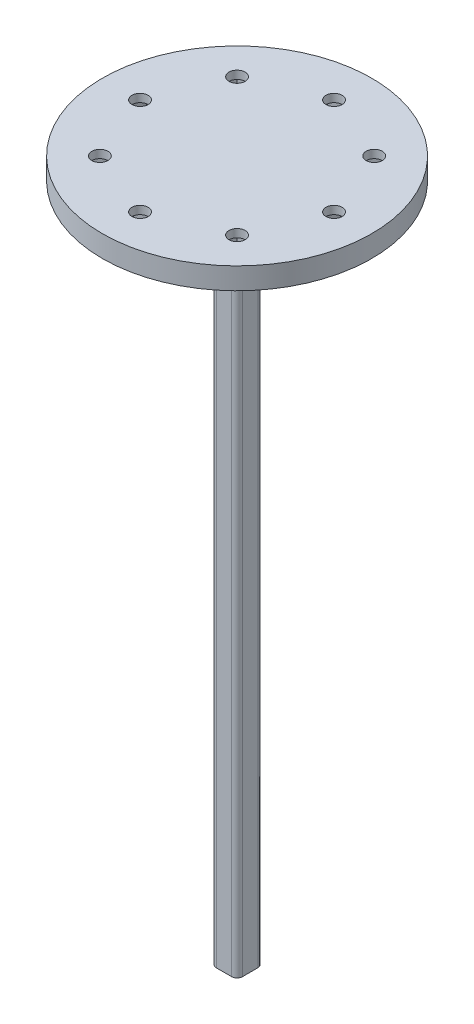
SolidWorks part; units mm, degrees
ref_plane "前视基准面" through (0, 0, 0) normal (0, 0, 1) x (1, 0, 0)
ref_plane "上视基准面" through (0, 0, 0) normal (0, 1, 0) x (1, 0, 0)
ref_plane "右视基准面" through (0, 0, 0) normal (1, 0, 0) x (0, 0, -1)
sketch "草图1" plane through (0, 0, 0) normal (0, 1, 0) x (1, 0, 0)
  circle A0 centre (0, 0) radius 20
  dimension "D1" = 40
extrude "凸台-拉伸1" add sketch "草图1" along normal blind 4
sketch "草图2" plane through (0, 0, 0) normal (0, -1, 0) x (1, 0, 0)
  circle A0 centre (0, 0) radius 7.4071
extrude "凸台-拉伸2" add sketch "草图2" along normal blind 8
sketch "草图3" plane through (0, -8, 0) normal (0, -1, 0) x (1, 0, 0)
  line L1 (-2.425, -2.425) -> (2.425, -2.425)
  line L2 (-2.425, -2.425) -> (-2.425, 2.425)
  line L3 (-2.425, 2.425) -> (2.425, 2.425)
  line L4 (2.425, -2.425) -> (2.425, 2.425)
  line L5 (-2.425, -2.425) -> (2.425, 2.425) construction
  line L6 (-2.425, 2.425) -> (2.425, -2.425) construction
  point P0 (0, 0)
  dimension "D1" = 4.85
  dimension "D2" = 4.85
extrude "凸台-拉伸3" add sketch "草图3" along normal blind 118
sketch "草图5" plane through (0, 4, 0) normal (0, 1, 0) x (1, 0, 0)
  circle A0 centre (0, 0) radius 25
  dimension "D1" = 50
extrude "凸台-拉伸4" add sketch "草图5" against normal blind 4
sketch "草图6" plane through (0, 0, 0) normal (0, -1, 0) x (1, 0, 0)
  line L3 (21.2332, 0) -> (19.6166, 2.8)
  line L4 (19.6166, 2.8) -> (16.3834, 2.8)
  line L5 (16.3834, 2.8) -> (14.7668, 0)
  line L6 (14.7668, 0) -> (16.3834, -2.8)
  line L7 (16.3834, -2.8) -> (19.6166, -2.8)
  line L8 (19.6166, -2.8) -> (21.2332, 0)
  circle A0 centre (18, 0) radius 2.8 construction
  dimension "D1" = 5.6
extrude "切除-拉伸1" cut sketch "草图6" against normal blind 2.5
sketch "草图7" plane through (0, 2.5, 0) normal (0, -1, 0) x (1, 0, 0)
  circle A0 centre (18, 0) radius 1.5
  dimension "D1" = 3
extrude "切除-拉伸2" cut sketch "草图7" against normal blind 2.5
pattern_circular "阵列(圆周)1" count 8 over 360 about axis through (0, 0, 0) along (0, 1, 0) of "切除-拉伸1", "切除-拉伸2"
fillet "圆角1" radius 1 4 edges at (2.425, -67, -2.425) (2.425, -67, 2.425) (-2.425, -67, 2.425) (-2.425, -67, -2.425)
sketch "草图9" plane through (0, 0, 0) normal (0, 1, 0) x (1, 0, 0)
  circle A0 centre (53.4876, 0) radius 25
  dimension "D1" = 50
extrude "凸台-拉伸5" add sketch "草图9" along normal blind 4 separate body
sketch "草图10" plane through (0, 0, 0) normal (0, -1, 0) x (1, 0, 0)
  circle A0 centre (53.4876, 0) radius 5.5
  dimension "D1" = 11
extrude "凸台-拉伸6" add sketch "草图10" along normal blind 8
sketch "草图11" plane through (0, -8, 0) normal (0, -1, 0) x (1, 0, 0)
  line L2 (51.0626, -2.425) -> (55.9126, -2.425)
  line L3 (51.0626, -2.425) -> (51.0626, 2.425)
  line L4 (51.0626, 2.425) -> (55.9126, 2.425)
  line L5 (55.9126, -2.425) -> (55.9126, 2.425)
  line L6 (51.0626, -2.425) -> (55.9126, 2.425) construction
  line L7 (51.0626, 2.425) -> (55.9126, -2.425) construction
  dimension "D1" = 4.85
  dimension "D2" = 4.85
extrude "凸台-拉伸7" add sketch "草图11" along normal blind 118
sketch "草图12" plane through (0, -126, 0) normal (0, -1, 0) x (1, 0, 0)
  line L3 (38.7207, 0) -> (37.1041, 2.8)
  line L4 (37.1041, 2.8) -> (33.871, 2.8)
  line L5 (33.871, 2.8) -> (32.2544, 0)
  line L6 (32.2544, 0) -> (33.871, -2.8)
  line L7 (33.871, -2.8) -> (37.1041, -2.8)
  line L8 (37.1041, -2.8) -> (38.7207, 0)
  circle A0 centre (35.4876, 0) radius 2.8 construction
  dimension "D3" = 5.6
extrude "切除-拉伸7" cut sketch "草图12" against normal blind 128.5
sketch "草图13" plane through (0, 2.5, 0) normal (0, -1, 0) x (1, 0, 0)
  circle A0 centre (35.4876, 0) radius 1.5
  dimension "D1" = 3
extrude "切除-拉伸8" cut sketch "草图13" against normal blind 128.5
pattern_circular "阵列(圆周)2" count 8 over 360 about axis through (53.4876, 0, 0) along (0, 1, 0) of "切除-拉伸8", "切除-拉伸7"
fillet "圆角2" radius 1 4 edges at (51.0626, -67, -2.425) (55.9126, -67, -2.425) (51.0626, -67, 2.425) (55.9126, -67, 2.425)
sketch "草图14" plane through (0, -8, 0) normal (0, -1, 0) x (1, 0, 0)
  circle A0 centre (0, 0) radius 5.5
  circle A1 centre (0, 0) radius 7.4071
  dimension "D1" = 11
extrude "切除-拉伸9" cut sketch "草图14" against normal blind 8
sketch "草图15" plane through (0, 4, 0) normal (0, 1, 0) x (1, 0, 0)
  line L0 (26.4113, 29.4385) -> (26.4113, -29.4385)
  line L1 (26.4113, 29.4385) -> (80.5638, 29.4385)
  line L2 (26.4113, -29.4385) -> (80.5638, -29.4385)
  line L3 (80.5638, 29.4385) -> (80.5638, -29.4385)
  line L4 (26.4113, 29.4385) -> (80.5638, -29.4385) construction
  line L5 (26.4113, -29.4385) -> (80.5638, 29.4385) construction
  point P1 (53.4876, 0)
extrude "切除-拉伸10" cut sketch "草图15" against normal blind 130
